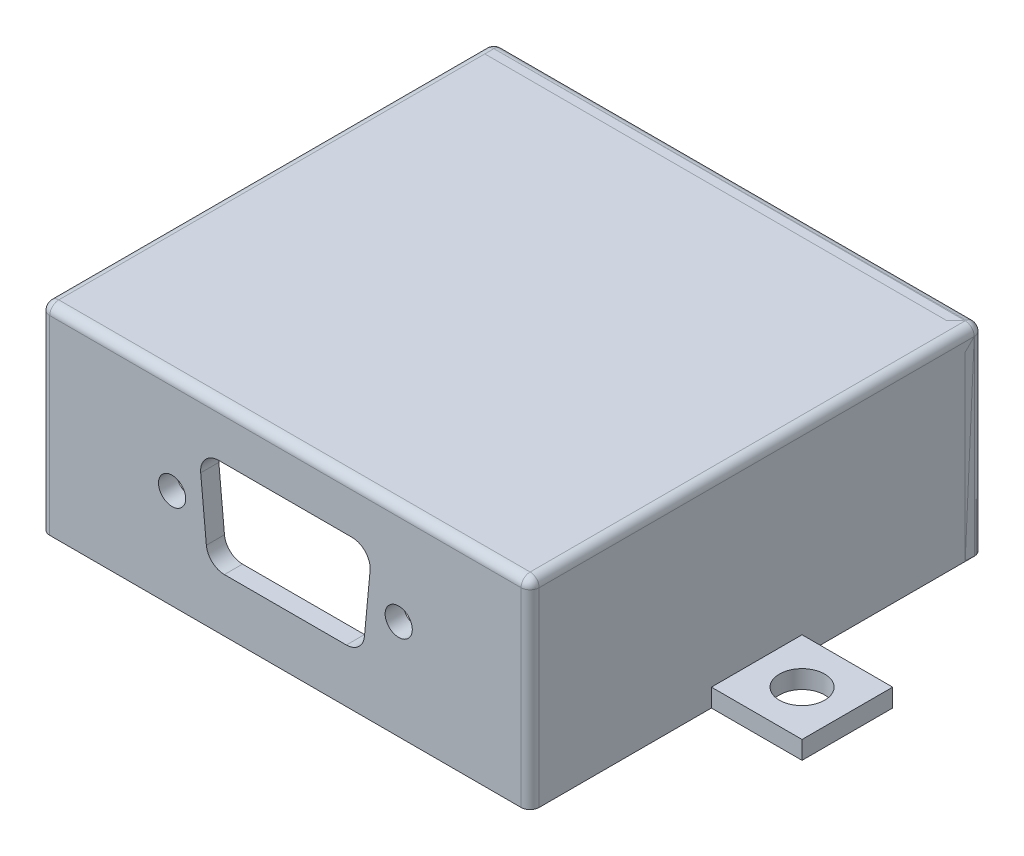
SolidWorks part; units mm, degrees
ref_plane "Front Plane" through (0, 0, 0) normal (0, 0, 1) x (1, 0, 0)
ref_plane "Top Plane" through (0, 0, 0) normal (0, 1, 0) x (1, 0, 0)
ref_plane "Right Plane" through (0, 0, 0) normal (1, 0, 0) x (0, 0, -1)
sketch "Sketch1" plane through (0, 0, 0) normal (0, 0, 1) x (1, 0, 0)
  line L0 (17.6476, 16.4884) -> (32.3524, 16.4884)
  line L1 (0, 0) -> (50, 0)
  line L2 (0, 0) -> (0, 20)
  line L3 (0, 20) -> (50, 20)
  line L4 (50, 0) -> (50, 20)
  line L5 (25, 20) -> (25, 0) construction
  line L6 (0, 10) -> (50, 10) construction
  line L7 (25, -5.2012) -> (25, 10) construction
  line L8 (18.2701, 5.889) -> (31.7299, 5.889)
  line L9 (34.55, 16.4884) -> (34.55, -3.7977) construction
  line L10 (15.45, 16.4884) -> (15.45, 3.0059) construction
  line L11 (34.3436, 14.3006) -> (33.721, 7.7012)
  line L12 (15.6564, 14.3006) -> (16.279, 7.7012)
  line L13 (15.45, 16.4884) -> (15.45, 17.0245) construction
  line L14 (12.4977, 11.0009) -> (37.5023, 11.0009) construction
  arc A0 (33.721, 7.7012) -> (31.7299, 5.889) centre (31.7299, 7.889) cw
  arc A1 (18.2701, 5.889) -> (16.279, 7.7012) centre (18.2701, 7.889) cw
  arc A2 (34.3436, 14.3006) -> (32.3524, 16.4884) centre (32.3524, 14.4884) ccw
  arc A3 (15.6564, 14.3006) -> (17.6476, 16.4884) centre (17.6476, 14.4884) cw
  circle A4 centre (12.4977, 11.0009) radius 1.5
  circle A5 centre (37.5023, 11.0009) radius 1.5
  point P8 (25, 16.4884)
  point P12 (15.9677, 11.0009)
  point P14 (34.0323, 11.0009)
  point P320 (25, 10)
  dimension "D3" = 2
  dimension "D5" = 3
  dimension "D9" = 3
  dimension "D1" = 20
  dimension "D2" = 50
  dimension "D4" = 7.3524
  dimension "D6" = 3.47
  dimension "D7" = 3.47
  dimension "D8" = 10.5994
  dimension "D10" = 25.0046
  dimension "D11" = 1.0009
  dimension "D12" = 4.111
extrude "Boss-Extrude1" add sketch "Sketch1" along normal blind 2
sketch "Sketch2" plane through (0, 0, 2) normal (0, 0, 1) x (1, 0, 0)
  line L0 (0, 20) -> (0, 0) construction
  line L2 (-2, 0) -> (-2, 22)
  line L3 (-2, 22) -> (52, 22)
  line L4 (52, 0) -> (52, 22)
  line L5 (50, 20) -> (0, 20) construction
  line L7 (50, 0) -> (50, 20) construction
  line L8 (-2, 0) -> (0, 0)
  line L9 (0, 0) -> (50, 0)
  line L10 (0, 0) -> (0, 20)
  line L11 (0, 20) -> (50, 20)
  line L12 (50, 0) -> (50, 20)
  line L13 (50, 0) -> (52, 0)
  line L14 (0, 0) -> (0, 20)
  line L15 (0, 0) -> (0, 20)
  line L16 (0, 20) -> (50, 20)
  line L17 (50, 20) -> (50, 0)
  line M5 (0, 20) -> (0, 0)
  line M7 (50, 0) -> (50, 20)
  line M8 (50, 20) -> (0, 20)
  dimension "D1" = 2
  dimension "D2" = 2
  dimension "D4" = 2
extrude "Boss-Extrude3" add sketch "Sketch2" against normal blind 50 contours L13 L4 L3 L2 L8 M7 M5 M8
sketch "Sketch4" plane through (0, 0, -48) normal (0, 0, -1) x (-1, 0, 0)
  line L1 (-52, 22) -> (2, 22)
  line L2 (-52, 22) -> (-52, 0)
  line L3 (-52, 0) -> (2, 0)
  line L4 (2, 22) -> (2, 0)
  circle A0 centre (-24, 10) radius 5
  dimension "D1" = 10
  dimension "D2" = 10
  dimension "D3" = 26
extrude "Boss-Extrude4" add sketch "Sketch4" against normal blind 2 separate body
ref_plane "Plane1" through (0, 0, -23) normal (0, 0, 1) x (1, 0, 0)
sketch "Sketch5" plane through (0, 0, -23) normal (0, 0, 1) x (1, 0, 0)
  line L1 (-2, 0) -> (-12, 0)
  line L2 (-2, 0) -> (-2, 2)
  line L3 (-2, 2) -> (-12, 2)
  line L4 (-12, 0) -> (-12, 2)
  line L5 (52, 0) -> (62, 0)
  line L6 (52, 0) -> (52, 2)
  line L7 (52, 2) -> (62, 2)
  line L8 (62, 0) -> (62, 2)
  dimension "D1" = 2
  dimension "D2" = 10
  dimension "D3" = 10
  dimension "D4" = 2
extrude "Boss-Extrude5" add sketch "Sketch5" along normal mid plane 10
fillet "Fillet1" radius 1 8 edges at (-2, 11, -48) (52, 11, -48) (52, 11, 2) (25, 22, -48) (52, 22, -23) (-2, 22, -23) (25, 22, 2) (-2, 11, 2)
fillet "Fillet2" radius 1 6 edges at (25, 22, -48) (-2, 11, -48) (25, 0, -48) (52, 11, -48) (52, 22, -47) (-2, 22, -47)
sketch "Sketch6" plane through (0, 2, 0) normal (0, 1, 0) x (1, 0, 0)
  line L0 (-11.55, 23) -> (11.55, 23) construction
  line L2 (-2, 18) -> (-2, 28) construction
  line L3 (52, 18) -> (52, 28) construction
  circle A0 centre (-7, 23) radius 2.5
  circle A1 centre (57, 23) radius 2.5
  dimension "D1" = 5
  dimension "D2" = 5
  dimension "D3" = 5
  dimension "D4" = 5
extrude "Cut-Extrude1" cut sketch "Sketch6" against normal blind 2
